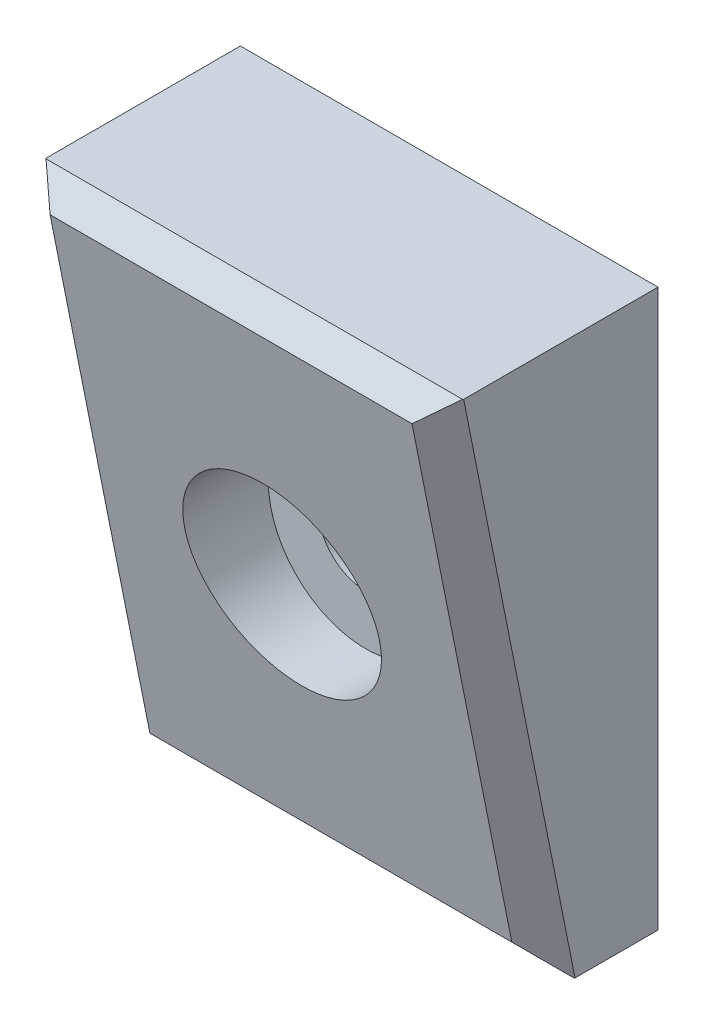
SolidWorks part; units mm, degrees
ref_plane "Front Plane" through (0, 0, 0) normal (0, 0, 1) x (1, 0, 0)
ref_plane "Top Plane" through (0, 0, 0) normal (0, 1, 0) x (1, 0, 0)
ref_plane "Right Plane" through (0, 0, 0) normal (1, 0, 0) x (0, 0, -1)
sketch "Sketch1" plane through (0, 0, 0) normal (0, 0, 1) x (1, 0, 0)
  line L1 (7.5, -10) -> (-7.5, -10)
  line L2 (7.5, -10) -> (7.5, 10)
  line L3 (7.5, 10) -> (-7.5, 10)
  line L4 (-7.5, -10) -> (-7.5, 10)
  line L5 (7.5, -10) -> (-7.5, 10) construction
  line L6 (7.5, 10) -> (-7.5, -10) construction
  circle A0 centre (0, 0) radius 1.7
  point P0 (0, 0)
  dimension "D3" = 3.4
  dimension "D1" = 15
  dimension "D2" = 20
extrude "Boss-Extrude1" add sketch "Sketch1" along normal blind 8
sketch "Sketch2" plane through (0, 0, 8) normal (0, 0, 1) x (1, 0, 0)
  circle A0 centre (0, 0) radius 3.5
  dimension "D1" = 7
extrude "Cut-Extrude1" cut sketch "Sketch2" against normal offset from surface (5 mm away) 3 up to face at (0, 0, 0)
sketch "Sketch3" plane through (7.5, 0, 0) normal (1, 0, 0) x (0, 0, -1)
  line L0 (-8, 10) -> (-4, -10)
  line L1 (-8, -10) -> (0, -10) construction
  line L2 (-4, -10) -> (-8, -10)
  line L3 (-8, -10) -> (-8, 10)
extrude "Cut-Extrude2" cut sketch "Sketch3" against normal through all
chamfer "Chamfer1" distance 1 angle 45 4 edges at (0, 10, 8) (-7.5, 0, 6) (0, -10, 4) (7.5, 0, 6)
